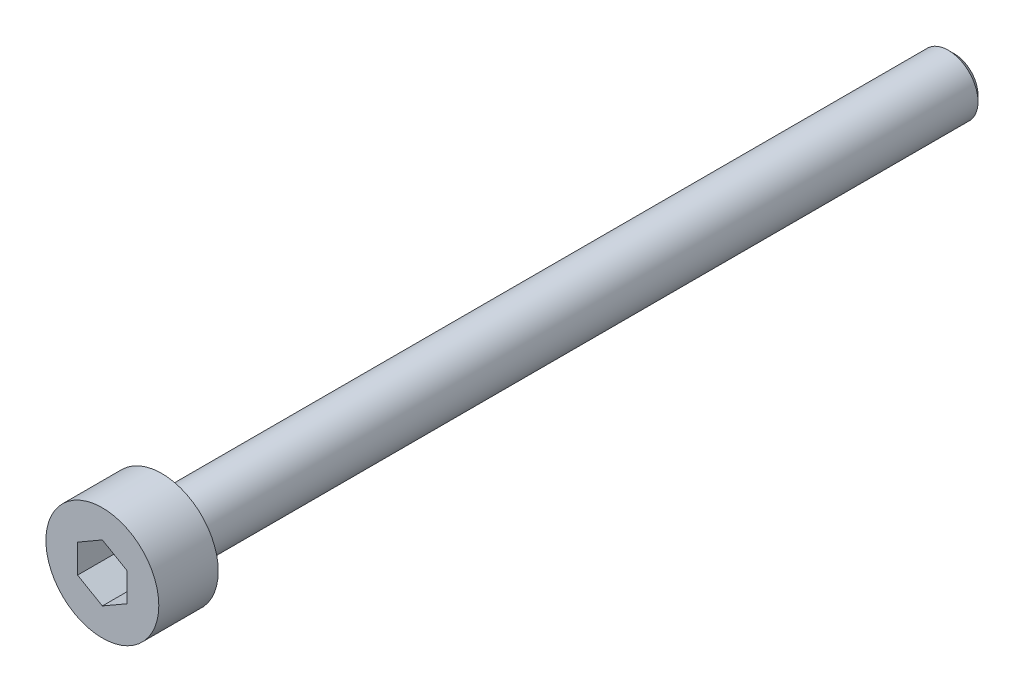
SolidWorks part; units mm, degrees
ref_plane "Front Plane" through (0, 0, 0) normal (0, 0, 1) x (1, 0, 0)
ref_plane "Top Plane" through (0, 0, 0) normal (0, 1, 0) x (1, 0, 0)
ref_plane "Right Plane" through (0, 0, 0) normal (1, 0, 0) x (0, 0, -1)
sketch "Sketch1" plane through (0, 0, 0) normal (0, 0, 1) x (1, 0, 0)
  circle A0 centre (0, 0) radius 2.85
  dimension "D1" = 5.7
extrude "Boss-Extrude1" add sketch "Sketch1" along normal blind 3
sketch "Sketch2" plane through (0, 0, 0) normal (0, 0, -1) x (-1, 0, 0)
  circle A0 centre (0, 0) radius 1.5
  dimension "D1" = 3
extrude "Boss-Extrude2" add sketch "Sketch2" along normal blind 40
chamfer "Chamfer1" distance 0.3 angle 45 1 edges at (-1.5, 0, -40)
sketch "Sketch3" plane through (0, 0, 3) normal (0, 0, 1) x (1, 0, 0)
  line L1 (0, 1.4434) -> (-1.25, 0.7217)
  line L2 (-1.25, 0.7217) -> (-1.25, -0.7217)
  line L3 (-1.25, -0.7217) -> (0, -1.4434)
  line L4 (0, -1.4434) -> (1.25, -0.7217)
  line L5 (1.25, -0.7217) -> (1.25, 0.7217)
  line L6 (1.25, 0.7217) -> (0, 1.4434)
  circle A0 centre (0, 0) radius 1.25 construction
  dimension "D1" = 2.5
extrude "Cut-Extrude1" cut sketch "Sketch3" against normal blind 2
